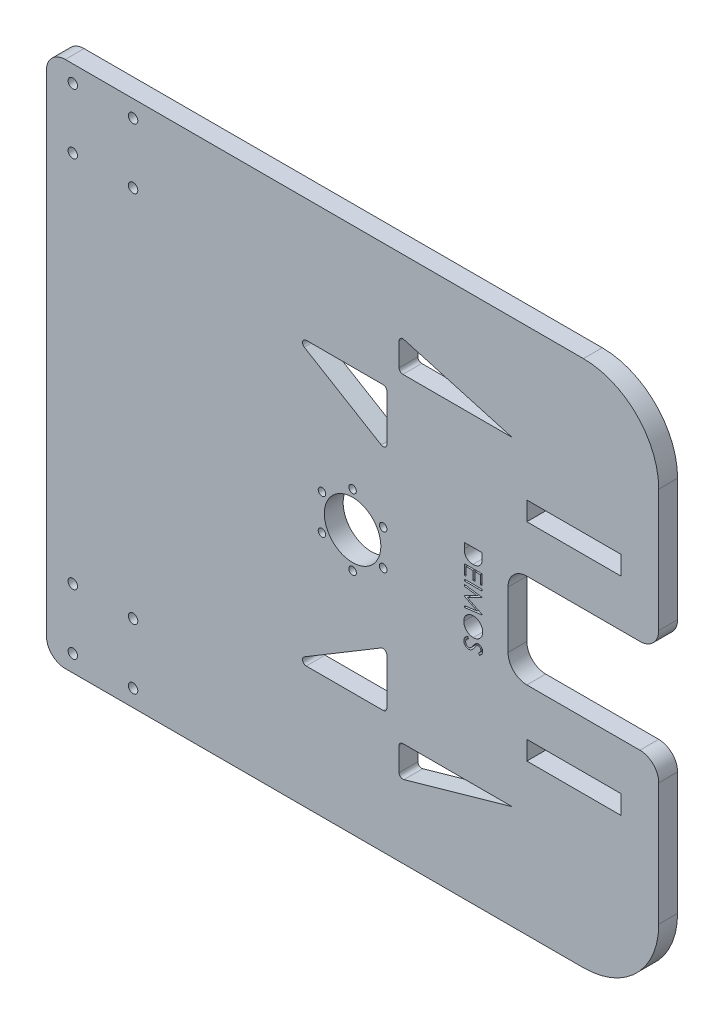
SolidWorks part; units mm, degrees
material "6061-T6 (SS)"
ref_plane "Front Plane" through (0, 0, 0) normal (0, 0, 1) x (1, 0, 0)
ref_plane "Top Plane" through (0, 0, 0) normal (0, 1, 0) x (1, 0, 0)
ref_plane "Right Plane" through (0, 0, 0) normal (1, 0, 0) x (0, 0, -1)
sketch "Sketch1" plane through (0, 0, 0) normal (0, 0, 1) x (1, 0, 0)
  line L53 (-21.3462, 140) -> (303.6538, 140)
  line L54 (-21.3462, 140) -> (-21.3462, 60)
  line L56 (-21.3462, 100) -> (303.6538, 100) construction
  line L57 (-21.3462, 60) -> (303.6538, 60)
  line L70 (141.1538, 0) -> (303.6538, 0) construction
  line L72 (303.6538, 140) -> (303.6538, 60)
  line L108 (-21.3462, 140) -> (303.6538, 140)
  line L109 (-21.3462, 60) -> (303.6538, 60)
  line L110 (-21.3462, -100) -> (303.6538, -100) construction
  line L111 (-21.3462, -60) -> (303.6538, -60)
  line L112 (-21.3462, -140) -> (303.6538, -140)
  line L124 (303.6538, -140) -> (303.6538, -60)
  line L129 (-21.3462, -60) -> (303.6538, -60)
  line L131 (-21.3462, -140) -> (-21.3462, -60)
  line L132 (-21.3462, -140) -> (303.6538, -140)
  line L133 (-21.3462, 60) -> (303.6538, 60)
  line L134 (-21.3462, 60) -> (-21.3462, -60)
  line L135 (303.6538, 60) -> (303.6538, -60)
  line L136 (-21.3462, -60) -> (303.6538, -60)
  line L139 (233.6538, -60) -> (283.6538, -60)
  line L140 (233.6538, -60) -> (233.6538, -50)
  line L141 (283.6538, -60) -> (283.6538, -50)
  line L142 (233.6538, -50) -> (283.6538, -50)
  line L143 (233.6538, 60) -> (283.6538, 60)
  line L144 (233.6538, 60) -> (233.6538, 50)
  line L145 (283.6538, 60) -> (283.6538, 50)
  line L146 (233.6538, 50) -> (283.6538, 50)
  circle A0 centre (141.1538, 0) radius 15
  circle A1 centre (141.1538, 0) radius 18.75 construction
  circle A2 centre (141.1538, 18.75) radius 2
  circle A12 centre (157.3918, 9.375) radius 2
  circle A13 centre (157.3918, -9.375) radius 2
  circle A14 centre (141.1538, -18.75) radius 2
  circle A15 centre (124.9159, -9.375) radius 2
  circle A16 centre (124.9159, 9.375) radius 2
  point P35 (141.1538, 0)
  point P42 (141.1538, -60)
  point P44 (-21.3462, 0)
  dimension "D7" = 280
  dimension "D2" = 20
  dimension "D8" = 120
  dimension "D10" = 10
  dimension "D5" = 4
  dimension "D6" = 6
  dimension "D3" = 30
  dimension "D4" = 37.5
  dimension "D13" = 325
  dimension "D9" = 50
  dimension "D14" = 20
extrude "Boss-Extrude1" add sketch "Sketch1" along normal blind 10
fillet "Fillet1" radius 10 2 edges at (-21.3462, -140, 5) (-21.3462, 140, 5)
fillet "Fillet2" radius 40 2 edges at (303.6538, -140, 5) (303.6538, 140, 5)
sketch "Sketch4" plane through (0, 0, 0) normal (0, 0, 1) x (1, 0, 0)
  line L0 (303.6538, 25) -> (223.6538, 25)
  line L1 (303.6538, 100) -> (303.6538, -100) construction
  line L2 (223.6538, 25) -> (223.6538, -25)
  line L3 (223.6538, -25) -> (303.6538, -25)
  line L4 (303.6538, 25) -> (303.6538, -25)
  line L5 (109.345, -74.8594) -> (159.345, -44.8594)
  line L6 (159.345, -44.8594) -> (159.345, -74.8594)
  line L7 (159.345, -74.8594) -> (109.345, -74.8594)
  line L8 (165.8478, -84.8594) -> (225.8478, -84.8594)
  line L9 (225.8478, -84.8594) -> (165.8478, -101.8594)
  line L10 (165.8478, -101.8594) -> (165.8478, -84.8594)
  line L11 (-21.3462, 0) -> (303.6538, 0) construction
  line L13 (-21.3462, 130) -> (-21.3462, -130) construction
  line L14 (159.345, 44.8594) -> (159.345, 74.8594)
  line L15 (159.345, 74.8594) -> (109.345, 74.8594)
  line L16 (109.345, 74.8594) -> (159.345, 44.8594)
  line L17 (225.8478, 84.8594) -> (165.8478, 101.8594)
  line L18 (165.8478, 101.8594) -> (165.8478, 84.8594)
  line L19 (165.8478, 84.8594) -> (225.8478, 84.8594)
  point P4 (303.6538, 0)
  dimension "D1" = 25
  dimension "D2" = 50
  dimension "D3" = 80
  dimension "D4" = 10
  dimension "D5" = 30
  dimension "D6" = 17
  dimension "D7" = 50
  dimension "D8" = 60
extrude "Cut-Extrude5" cut sketch "Sketch4" along normal blind 10 contours L4 L3 L2 L0 | L10 L8 L9 | L7 L5 L6 | L14 L15 L16 | L17 L18 L19
fillet "Fillet4" radius 10 4 edges at (303.6538, -25, 5) (303.6538, 25, 5) (223.6538, -25, 5) (223.6538, 25, 5)
fillet "Fillet5" radius 2 10 edges at (159.345, 44.8594, 5) (109.345, 74.8594, 5) (159.345, 74.8594, 5) (165.8478, 84.8594, 5) (165.8478, 101.8594, 5) (165.8478, -101.8594, 5) (165.8478, -84.8594, 5) (159.345, -74.8594, 5) (159.345, -44.8594, 5) (109.345, -74.8594, 5)
sketch "Sketch6" plane through (0, 0, 10) normal (0, 0, 1) x (1, 0, 0)
  line L0 (200.4405, 140) -> (200.4405, -140) construction
  line L1 (-11.3462, 140) -> (263.6538, 140) construction
  line L2 (-11.3462, -140) -> (263.6538, -140) construction
sketch "Sketch8" plane through (0, 0, 10) normal (0, 0, 1) x (1, 0, 0)
  text T0 "DEIMOS" font "Century Gothic" height in points 36
extrude "Cut-Extrude7" cut sketch "Sketch8" against normal blind 34
sketch "Sketch9" plane through (0, 0, 10) normal (0, 0, 1) x (1, 0, 0)
  line L0 (-11.3462, -140) -> (263.6538, -140) construction
  line L4 (-21.3462, 0) -> (223.6538, 0) construction
  line L5 (-21.3462, 130) -> (-21.3462, -130) construction
  line L6 (223.6538, 15) -> (223.6538, -15) construction
  line L7 (-7.3462, 99) -> (24.6538, 131) construction
  line L8 (-7.3462, -131) -> (24.6538, -131) construction
  line L9 (-7.3462, -131) -> (-7.3462, -99) construction
  line L10 (-7.3462, -99) -> (24.6538, -99) construction
  line L11 (24.6538, -131) -> (24.6538, -99) construction
  line L12 (-7.3462, -131) -> (24.6538, -99) construction
  line L13 (-7.3462, -99) -> (24.6538, -131) construction
  line L14 (-7.3462, 131) -> (24.6538, 99) construction
  line L15 (24.6538, 131) -> (24.6538, 99) construction
  line L16 (-7.3462, 99) -> (24.6538, 99) construction
  line L17 (-7.3462, 131) -> (-7.3462, 99) construction
  line L18 (-7.3462, 131) -> (24.6538, 131) construction
  circle A2 centre (-7.3462, -99) radius 2.5
  circle A3 centre (24.6538, -99) radius 2.5
  circle A4 centre (-7.3462, -131) radius 2.5
  circle A5 centre (24.6538, -131) radius 2.5
  circle A6 centre (24.6538, 131) radius 2.5
  circle A7 centre (-7.3462, 131) radius 2.5
  circle A8 centre (24.6538, 99) radius 2.5
  circle A9 centre (-7.3462, 99) radius 2.5
  point P15 (8.6538, -115)
  point P32 (8.6538, 115)
  dimension "D4" = 5
  dimension "D1" = 25
  dimension "D3" = 32
  dimension "D7" = 30
extrude "Cut-Extrude8" cut sketch "Sketch9" against normal blind 10
